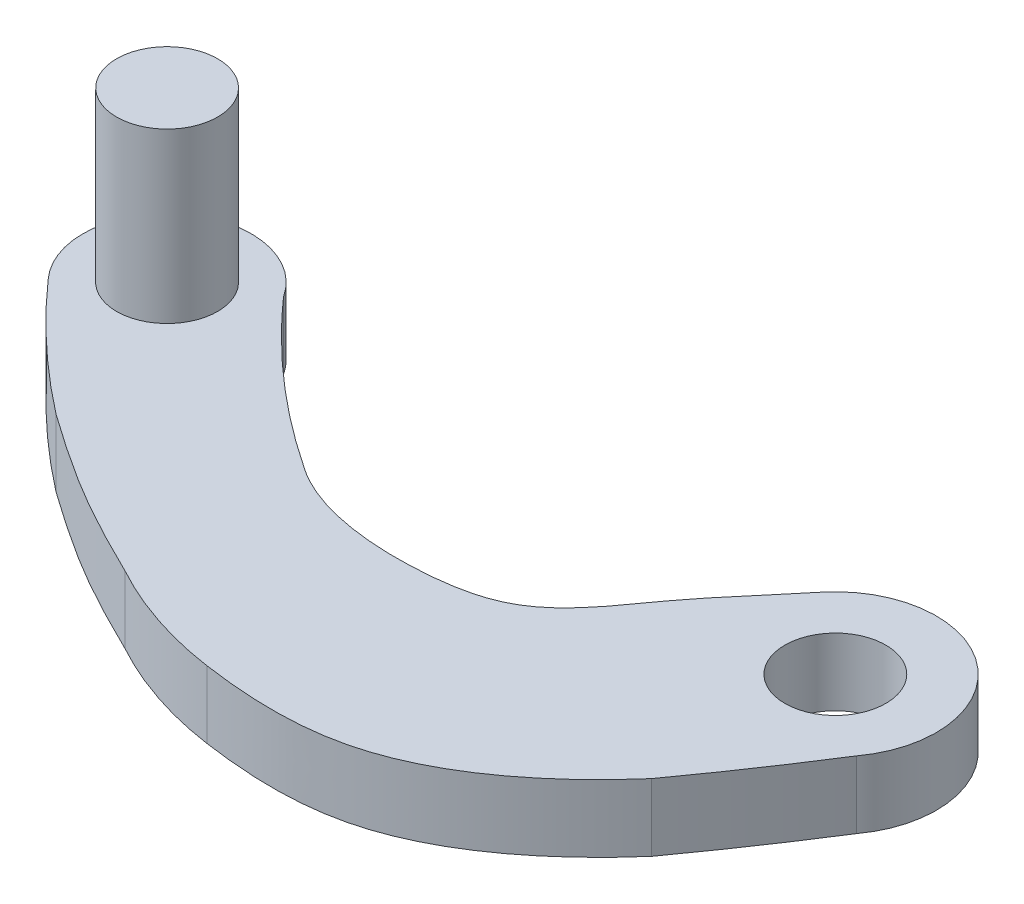
SolidWorks part; units mm, degrees
ref_plane "Alzado" through (0, 0, 0) normal (0, 0, 1) x (1, 0, 0)
ref_plane "Planta" through (0, 0, 0) normal (0, 1, 0) x (1, 0, 0)
ref_plane "Vista lateral" through (0, 0, 0) normal (1, 0, 0) x (0, 0, -1)
sketch "Croquis1" plane through (0, 0, 0) normal (0, 1, 0) x (1, 0, 0)
  arc A0 (2.0399, -2.1998) -> (-2.3346, 1.884) centre (0, 0) ccw
  arc A1 (-17.8973, 1.5111) -> (-21.839, -1.5351) centre (-19.9994, 0.1577) ccw
  spline S0 degree 3 poles (-2.3346, 1.884) (-2.9513, 1.1198) (-4.5093, -0.5633) (-5.9884, -3.1213) (-9.7773, -3.725) (-12.1085, -3.3491) (-13.2054, -2.5694) knots 0 0 0 0 0.210356 0.457411 0.578047 0.8709 0.8709 0.8709 0.8709
  spline S1 degree 3 poles (-0.0476, -5.4143) (-1.437, -7.008) (-4.4676, -9.495) (-8.1889, -9.3064) (-9.5549, -9.109) knots 0 0 0 0 0.60822 1 1 1 1
  spline S2 degree 2 poles (-9.5549, -9.109) (-11.4806, -8.8296) (-13.2054, -7.8865) knots 0 0 0 1 1 1
  spline S3 degree 2 poles (-13.2054, -2.5694) (-15.8194, -0.8338) (-17.8973, 1.5111) knots 0 0 0 1 1 1
  spline S4 degree 2 poles (-18.2577, -4.882) (-20.2061, -3.377) (-21.839, -1.5351) knots 0 0 0 1 1 1
  spline S5 degree 3 poles (-13.2054, -7.8865) (-14.0543, -7.4718) (-15.8067, -6.5809) (-17.4289, -5.4696) (-18.2577, -4.882) knots 0 0 0 0 0.481849 1 1 1 1
  spline S6 degree 2 poles (-0.0476, -5.4143) (1.2398, -3.6351) (2.4146, -1.7804) knots 0 0 0 1 1 1
  dimension "D1" = 6
  dimension "D2" = 5
  dimension "D4" = 6.5
  dimension "D3" = 20
  dimension "D5" = 6.5
  dimension "D6" = 13.9849
extrude "Saliente-Extruir1" add sketch "Croquis1" along normal blind 2
sketch "Croquis2" plane through (0, 2, 0) normal (0, 1, 0) x (1, 0, 0)
  circle A0 centre (0, 0) radius 1.5
  dimension "D1" = 3
extrude "Cortar-Extruir2" cut sketch "Croquis2" against normal blind 3
sketch "Croquis4" plane through (0, 2, 0) normal (0, 1, 0) x (1, 0, 0)
  circle A0 centre (-19.9994, 0.1577) radius 1.5
  dimension "D1" = 3
extrude "Saliente-Extruir3" add sketch "Croquis4" along normal blind 5
